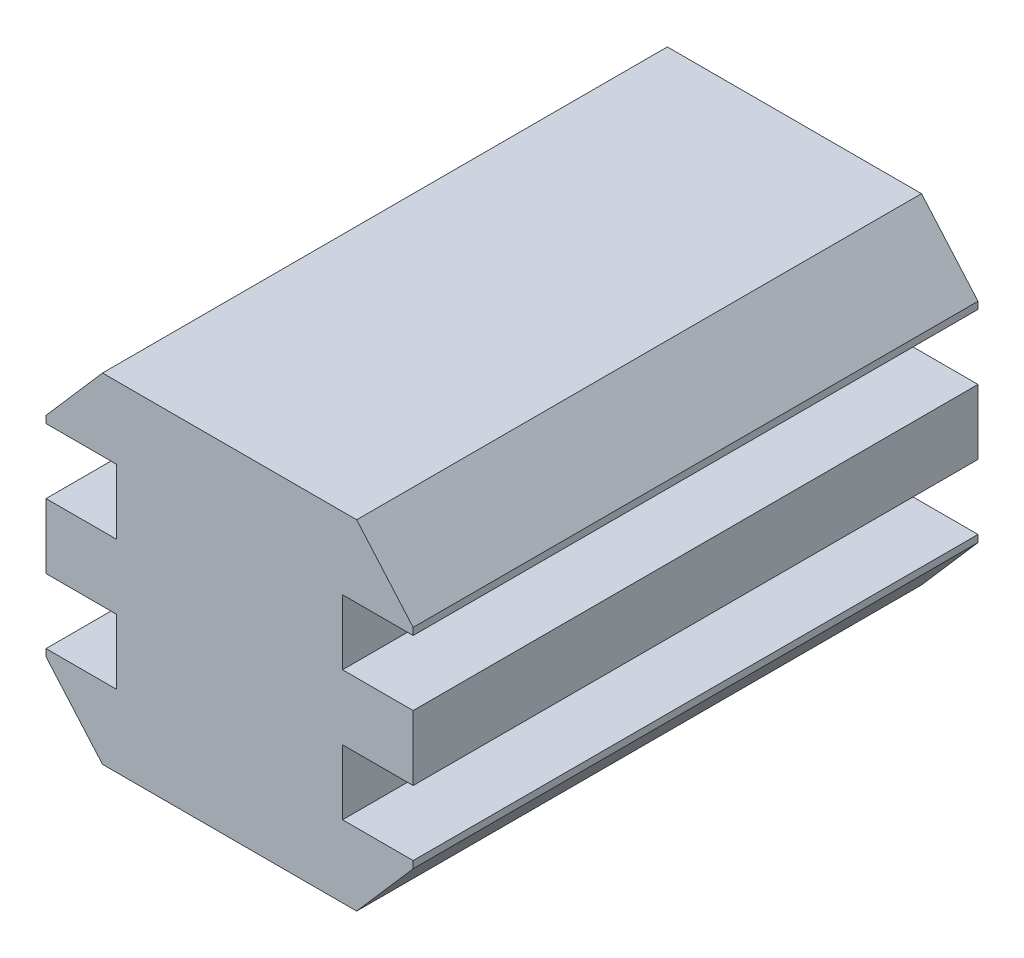
SolidWorks part; units mm, degrees
material "PE Alta Densidade"
ref_plane "Plano frontal" through (0, 0, 0) normal (0, 0, 1) x (1, 0, 0)
ref_plane "Plano superior" through (0, 0, 0) normal (0, 1, 0) x (1, 0, 0)
ref_plane "Plano direito" through (0, 0, 0) normal (1, 0, 0) x (0, 0, -1)
sketch "Esboço1" plane through (0, 0, 0) normal (0, 0, 1) x (1, 0, 0)
  line L0 (-4.5, -6) -> (4.5, -6)
  line L1 (-4.5, -6) -> (-6.5, -3.7)
  line L2 (6.5, -3.7) -> (6.5, -3.45)
  line L3 (6.5, -3.45) -> (4, -3.45)
  line L4 (4, -3.45) -> (4, -1.15)
  line L5 (4, -1.15) -> (6.5, -1.15)
  line L6 (6.5, -1.15) -> (6.5, 1.15)
  line L7 (4, 1.15) -> (6.5, 1.15)
  line L8 (4, 3.45) -> (4, 1.15)
  line L9 (6.5, 3.45) -> (4, 3.45)
  line L10 (6.5, 3.7) -> (6.5, 3.45)
  line L11 (4.5, -6) -> (6.5, -3.7)
  line L12 (4.5, 6) -> (6.5, 3.7)
  line L13 (0, 14.388) -> (0, -9.624) construction
  line L14 (-4.5, 6) -> (4.5, 6)
  line L15 (-6.5, -3.7) -> (-6.5, -3.45)
  line L16 (-6.5, -3.45) -> (-4, -3.45)
  line L17 (-4, -3.45) -> (-4, -1.15)
  line L18 (-4, -1.15) -> (-6.5, -1.15)
  line L19 (-6.5, -1.15) -> (-6.5, 1.15)
  line L20 (-4.5, 6) -> (-6.5, 3.7)
  line L21 (-6.5, 3.7) -> (-6.5, 3.45)
  line L22 (-6.5, 3.45) -> (-4, 3.45)
  line L23 (-4, 3.45) -> (-4, 1.15)
  line L24 (-4, 1.15) -> (-6.5, 1.15)
  line L25 (-8.8286, 0) -> (11.4625, 0) construction
  point P0 (0, 0)
  point P1 (6.5, -6)
  point P17 (-6.5, -6)
  point P31 (6.5, 0)
  point P33 (0, -6)
  dimension "D1" = 12
  dimension "D2" = 13
  dimension "D3" = 2.3
  dimension "D4" = 2.3
  dimension "D5" = 0.25
  dimension "D6" = 8
  dimension "D7" = 9
extrude "Ressalto-extrusão1" add sketch "Esboço1" along normal blind 20
